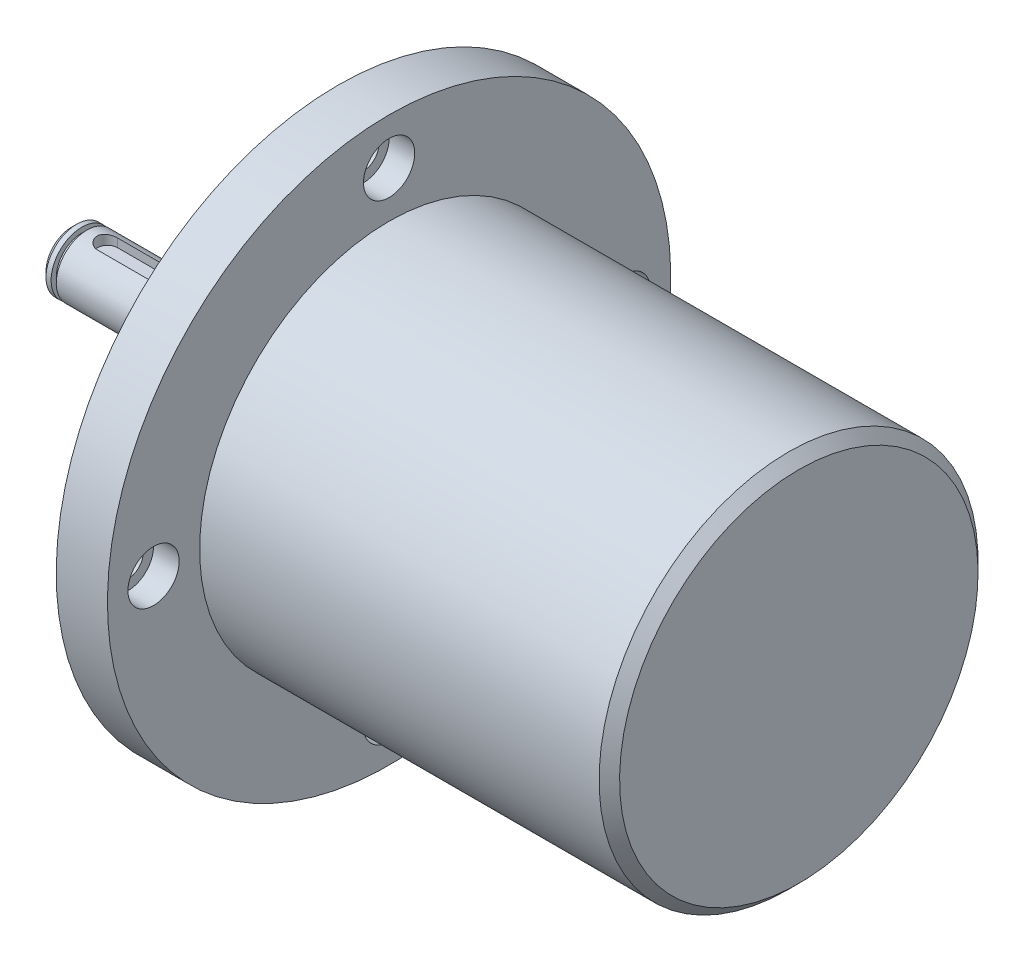
SolidWorks part; units mm, degrees
ref_plane "Plan de face" through (0, 0, 0) normal (0, 0, 1) x (1, 0, 0)
ref_plane "Plan de dessus" through (0, 0, 0) normal (0, 1, 0) x (1, 0, 0)
ref_plane "Plan de droite" through (0, 0, 0) normal (1, 0, 0) x (0, 0, -1)
ref_plane "Plan1" through (0, 4, 0) normal (0, 1, 0) x (1, 0, 0)
sketch "Esquisse1" plane through (0, 0, 0) normal (0, 0, 1) x (1, 0, 0)
  line L0 (0, 0) -> (0, 5)
  line L1 (0, 5) -> (1, 6)
  line L2 (1, 6) -> (2, 6)
  line L3 (2, 6) -> (2, 5)
  line L4 (2, 5) -> (3, 5)
  line L5 (3, 5) -> (3, 6)
  line L6 (3, 6) -> (30, 6)
  line L7 (30, 6) -> (30, 10)
  line L8 (30, 10) -> (49, 10)
  line L9 (49, 10) -> (49, 24)
  line L10 (49, 24) -> (50, 25)
  line L11 (50, 25) -> (52, 25)
  line L12 (52, 25) -> (52, 55)
  line L13 (52, 55) -> (62, 55)
  line L14 (62, 55) -> (62, 37)
  line L15 (62, 37) -> (140, 37)
  line L16 (140, 37) -> (142, 35)
  line L17 (142, 35) -> (142, 0)
  line L18 (142, 0) -> (0, 0)
  dimension "10" = 10
  dimension "D2" = 3
  dimension "D3" = 1
  dimension "D4" = 1
  dimension "D5" = 52
  dimension "D6" = 22
  dimension "D7" = 1
  dimension "D8" = 1
  dimension "D9" = 2
  dimension "D10" = 2
  dimension "D11" = 37
  dimension "D12" = 6
  dimension "D13" = 6
  dimension "D14" = 5
  dimension "D15" = 10
  dimension "D16" = 25
  dimension "D17" = 55
  dimension "D18" = 80
revolve "Révolution1" add sketch "Esquisse1" angle 360 about L18
sketch "Esquisse2" plane through (0, 0, 0) normal (0, 0, 1) x (1, 0, 0)
  line L0 (44.057, 46) -> (69.7309, 46)
  line L1 (69.7309, 46) -> (69.7309, 51)
  line L2 (69.7309, 51) -> (57, 51)
  line L3 (57, 51) -> (57, 49)
  line L4 (57, 49) -> (44.057, 49)
  line L5 (44.057, 49) -> (44.057, 46)
  line L6 (52, 55) -> (52, -55) construction
  dimension "D1" = 5
  dimension "D2" = 3
  dimension "D3" = 5
  dimension "D4" = 46
revolve "Enlèvement de matière-Révolution1" cut sketch "Esquisse2" angle 360 about L0
pattern_circular "Répétition circulaire1" count 4 every 90 about axis through (0, 0, 0) along (1, 0, 0) of "Enlèvement de matière-Révolution1"
sketch "Esquisse3" plane through (0, 4, 0) normal (0, 1, 0) x (1, 0, 0)
  line L0 (7, 0) -> (19, 0) construction
  line L1 (7, 2) -> (19, 2)
  line L2 (7, -2) -> (19, -2)
  arc A0 (7, 2) -> (7, -2) centre (7, 0) ccw
  arc A1 (19, -2) -> (19, 2) centre (19, 0) ccw
  point P3 (13, 0)
  dimension "D1" = 4
  dimension "D2" = 12
  dimension "D3" = 7
extrude "Enlèv. mat.-Extru.1" cut sketch "Esquisse3" along normal blind 10
